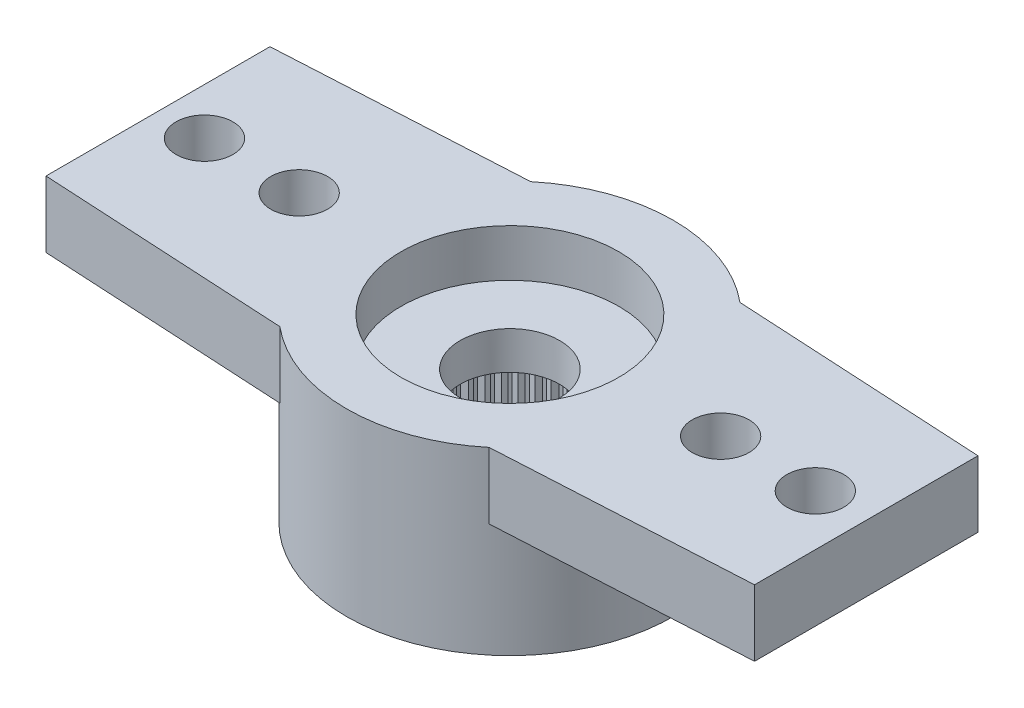
SolidWorks part; units mm, degrees
material "PVC Rígido"
ref_plane "Plano frontal" through (0, 0, 0) normal (0, 0, 1) x (1, 0, 0)
ref_plane "Plano superior" through (0, 0, 0) normal (0, 1, 0) x (1, 0, 0)
ref_plane "Plano direito" through (0, 0, 0) normal (1, 0, 0) x (0, 0, -1)
sketch "Esboço1" plane through (0, 0, 0) normal (0, 1, 0) x (1, 0, 0)
  line L0 (0, 0) -> (-14.05, 0) construction
  line L1 (-14.1591, 1.997) -> (-2.2091, 2.65)
  line L2 (-2.2091, -2.65) -> (-14.1591, -1.997)
  arc A0 (-2.2091, -2.65) -> (-2.2091, 2.65) centre (0, 0) ccw
  arc A1 (-14.1591, 1.997) -> (-14.1591, -1.997) centre (-14.05, 0) ccw
  dimension "D1" = 6.9
  dimension "D2" = 4
  dimension "D3" = 19.5
  dimension "D4" = 5.3
extrude "Ressalto-extrusão1" add sketch "Esboço1" against normal blind 1.4
sketch "Esboço2" plane through (0, -1.4, 0) normal (0, -1, 0) x (1, 0, 0)
  arc A0 (-2.2091, -2.65) -> (-2.2091, 2.65) centre (0, 0) ccw construction
  circle A1 centre (0, 0) radius 3.45
extrude "Ressalto-extrusão2" add sketch "Esboço2" along normal offset from surface (2.4 mm away) 3.8 up to face at (-7.242, 0, 0)
hole_wizard "Furo4" positions "Esboço9" profile "Esboço10" legacy end condition through all
sketch "Esboço9" plane through (0, 0, 0) normal (0, 1, 0) x (1, 0, 0)
  line L1 (-14.45, 0) -> (0, 0) construction
  arc A2 (-14.1591, 1.997) -> (-14.1591, -1.997) centre (-14.05, 0) ccw construction
  point P0 (-14.45, 0)
  point P19 (-16.05, 0)
  dimension "D1" = 1.6
sketch "Esboço10" plane through (-14.45, 0, 0) normal (1, 0, 0) x (0, 0, 1)
  line L0 (0, 0) -> (0, 3.8)
  line L1 (0, 3.8) -> (0.6, 3.8)
  line L2 (0.6, 3.8) -> (0.6, 0)
  line L3 (0.6, 0) -> (0, 0)
  line L4 (0, 110) -> (0, -10) construction
  dimension "Diameter" = 1.2
  dimension "Depth" = 3.8
pattern_linear "Padrão linear1" count 6 spacing 2 along (1, 0, 0) of "Furo4"
pattern_circular "PadrãoCircular2" count 2 over 360 about axis through (0, 0, 0) along (0, 1, 0) of "Ressalto-extrusão1", "Furo4", "Padrão linear1"
hole_wizard "Furo1" positions "Esboço3" profile "Esboço4" legacy
sketch "Esboço3" plane through (0, -3.8, 0) normal (0, -1, 0) x (-1, 0, 0)
  point P0 (0, 0)
sketch "Esboço4" plane through (0, -3.8, 0) normal (1, 0, 0) x (0, 0, -1)
  line L0 (0, 0) -> (0, 2)
  line L1 (0, 2) -> (2.475, 2)
  line L2 (2.475, 2) -> (2.475, 0)
  line L3 (2.475, 0) -> (0, 0)
  line L4 (0, 110) -> (0, -10) construction
  dimension "Diameter" = 4.95
  dimension "Depth" = 2
hole_wizard "Furo2" positions "Esboço5" profile "Esboço6" legacy
sketch "Esboço5" plane through (0, 0, 0) normal (0, 1, 0) x (1, 0, 0)
  point P0 (0, 0)
sketch "Esboço6" plane through (0, 0, 0) normal (1, 0, 0) x (0, 0, 1)
  line L0 (0, 0) -> (0, 1)
  line L1 (0, 1) -> (2.3, 1)
  line L2 (2.3, 1) -> (2.3, 0)
  line L3 (2.3, 0) -> (0, 0)
  line L4 (0, 110) -> (0, -10) construction
  dimension "Diameter" = 4.6
  dimension "Depth" = 1
hole_wizard "Furo3" positions "Esboço7" profile "Esboço8" legacy end condition through all
sketch "Esboço7" plane through (0, 0, 0) normal (0, 1, 0) x (1, 0, 0)
  point P0 (0, 0)
sketch "Esboço8" plane through (0, 0, 0) normal (1, 0, 0) x (0, 0, 1)
  line L0 (0, 0) -> (0, 3.8)
  line L1 (0, 3.8) -> (1.05, 3.8)
  line L2 (1.05, 3.8) -> (1.05, 0)
  line L3 (1.05, 0) -> (0, 0)
  line L4 (0, 110) -> (0, -10) construction
  dimension "Diameter" = 2.1
  dimension "Depth" = 3.8
sketch "Esboço11" plane through (0, -3.8, 0) normal (0, -1, 0) x (1, 0, 0)
  line L0 (-0.0981, 2.4731) -> (0, 2.375)
  line L1 (0, 2.375) -> (0.0981, 2.4731)
  line L2 (0, 0) -> (0, 2.475) construction
  circle A0 centre (0, 0) radius 2.375 construction
  circle A1 centre (0, 0) radius 2.475
  arc A2 (0.0981, 2.4731) -> (-0.0981, 2.4731) centre (0, 0) ccw
  dimension "D3" = 4.75
  dimension "D2" = 0.1
  dimension "D1" = 0
extrude "Ressalto-extrusão3" add sketch "Esboço11" against normal up to surface (2 mm away) up to face at (0, -1.8, 1.05)
pattern_circular "PadrãoCircular1" count 60 over 360 about axis through (0, 0, 0) along (0, 1, 0) of "Ressalto-extrusão3"
sketch "Sketch1" plane through (0, 0, 0) normal (0, 1, 0) x (1, 0, 0)
  line L1 (-17.1725, 6.0671) -> (18.2312, 6.0671)
  line L2 (-17.1725, 6.0671) -> (-17.1725, -5.905)
  line L3 (-17.1725, -5.905) -> (18.2312, -5.905)
  line L4 (18.2312, 6.0671) -> (18.2312, -5.905)
  line L5 (-7.432, 4.107) -> (7.5256, 4.107)
  line L6 (-7.432, 4.107) -> (-7.432, -4.0051)
  line L7 (-7.432, -4.0051) -> (7.5256, -4.0051)
  line L8 (7.5256, 4.107) -> (7.5256, -4.0051)
extrude "Cut-Extrude1" cut sketch "Sketch1" against normal blind 10
